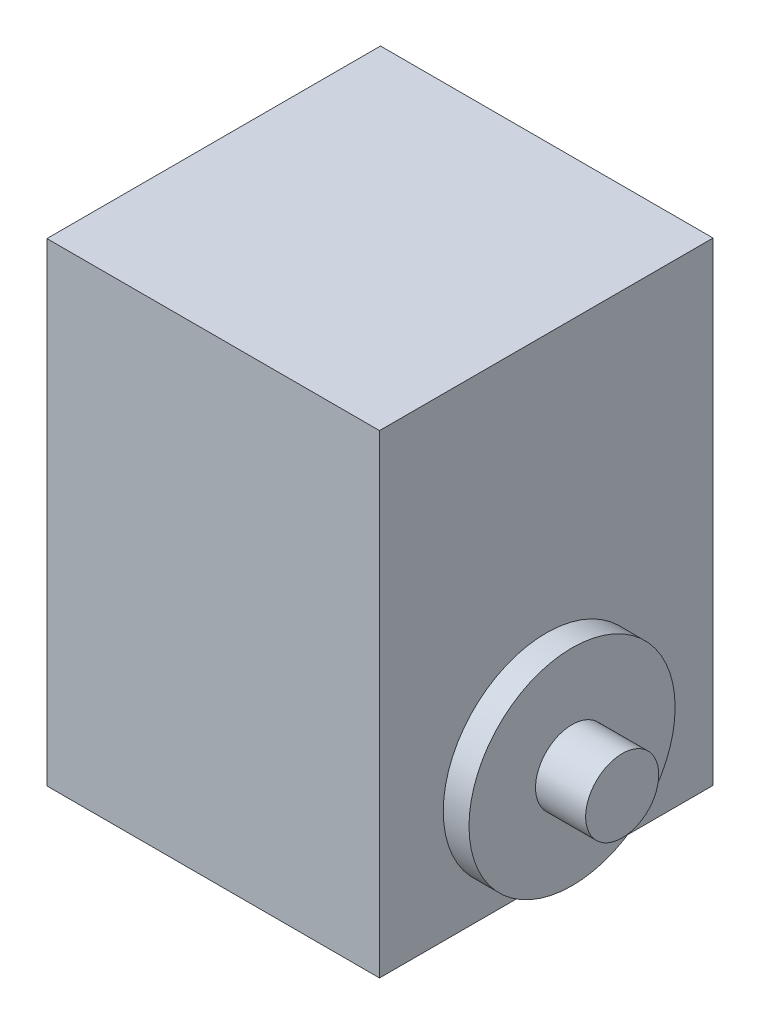
SolidWorks part; units mm, degrees
ref_plane "Front Plane" through (0, 0, 0) normal (0, 0, 1) x (1, 0, 0)
ref_plane "Top Plane" through (0, 0, 0) normal (0, 1, 0) x (1, 0, 0)
ref_plane "Right Plane" through (0, 0, 0) normal (1, 0, 0) x (0, 0, -1)
ref_plane "Plane1" through (0, -12, 0) normal (0, 1, 0) x (-1, 0, 0)
sketch "Sketch2" plane through (0, -12, 0) normal (0, 1, 0) x (-1, 0, 0)
  line L1 (-17.75, 17.8) -> (17.75, 17.8)
  line L2 (-17.75, 17.8) -> (-17.75, -17.8)
  line L3 (-17.75, -17.8) -> (17.75, -17.8)
  line L4 (17.75, 17.8) -> (17.75, -17.8)
  line L5 (-17.75, 17.8) -> (17.75, -17.8) construction
  line L6 (-17.75, -17.8) -> (17.75, 17.8) construction
  point P0 (0, 0)
  dimension "D2" = 35.6
  dimension "D3" = 35.5
extrude "Boss-Extrude1" add sketch "Sketch2" along normal blind 50.6
sketch "Sketch3" plane through (17.75, 0, 0) normal (1, 0, 0) x (0, 0, -1)
  line L0 (0, 0) -> (0, -12) construction
  line L1 (-17.8, -12) -> (17.8, -12) construction
  circle A0 centre (0, 0) radius 11
  dimension "D2" = 22
  dimension "D1" = 12
extrude "Boss-Extrude2" add sketch "Sketch3" along normal blind 2.75
sketch "Sketch4" plane through (20.5, 0, 0) normal (1, 0, 0) x (0, 0, -1)
  circle A0 centre (0, 0) radius 3.9
  dimension "D1" = 7.8
extrude "Boss-Extrude3" add sketch "Sketch4" along normal blind 5.35
ref_plane "Plane2" through (0, 13.3, 0) normal (0, 1, 0) x (-1, 0, 0)
mirror "Mirror1" about plane through (0, 0, 0) normal (1, 0, 0) of "Boss-Extrude3", "Boss-Extrude2"
